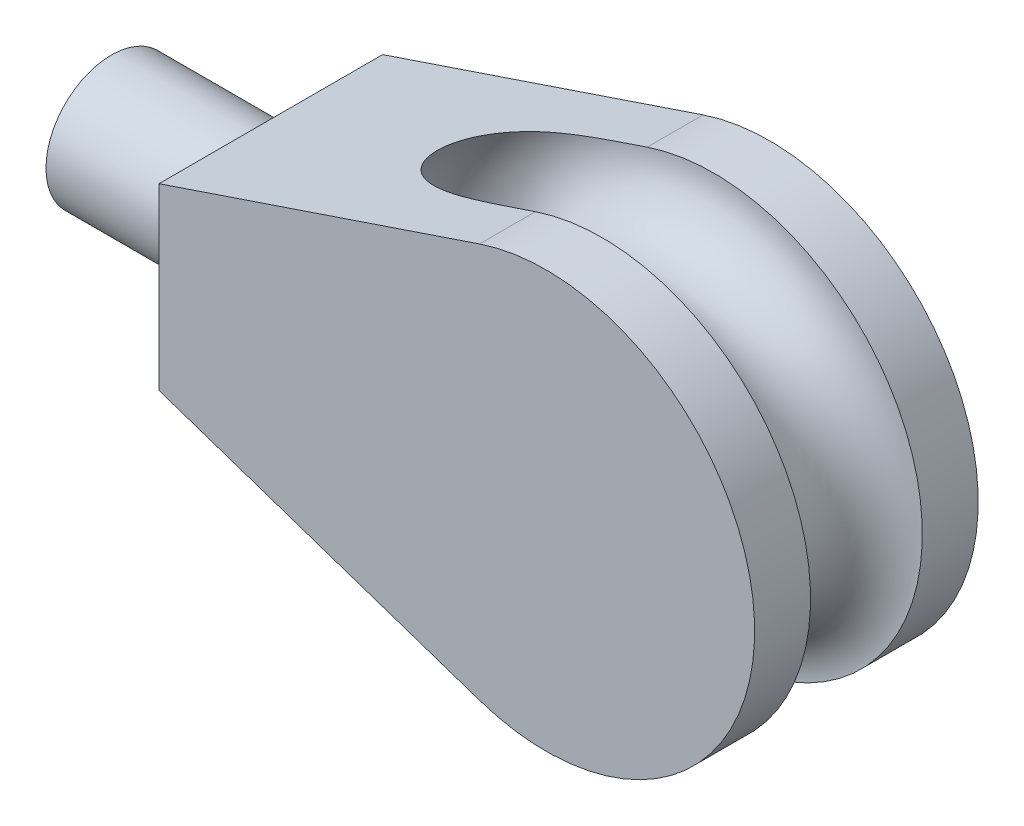
SolidWorks part; units mm, degrees
material "6061-T6 (SS)"
ref_plane "Front Plane" through (0, 0, 0) normal (0, 0, 1) x (1, 0, 0)
ref_plane "Top Plane" through (0, 0, 0) normal (0, 1, 0) x (1, 0, 0)
ref_plane "Right Plane" through (0, 0, 0) normal (1, 0, 0) x (0, 0, -1)
sketch "Sketch1" plane through (0, 0, 0) normal (0, 0, 1) x (1, 0, 0)
  line L0 (-27.4416, 6.35) -> (-27.4416, -6.35)
  line L1 (-27.4416, -6.35) -> (-4.722, -14.0084)
  line L2 (-27.4416, 6.35) -> (-4.722, 14.0084)
  arc A0 (-4.722, -14.0084) -> (-4.722, 14.0084) centre (0, 0) ccw
  point P5 (-27.4416, 0)
  dimension "D1" = 29.5656
  dimension "D2" = 12.7
  dimension "D3" = 108.628
extrude "Boss-Extrude1" add sketch "Sketch1" along normal mid plane 15.8496
sketch "Sketch2" plane through (-27.4416, 0, 0) normal (-1, 0, 0) x (0, 0, 1)
  circle A0 centre (0, 0) radius 4.6355
  dimension "D1" = 9.271
extrude "Boss-Extrude2" add sketch "Sketch2" along normal blind 11.303
sketch "Sketch6" plane through (0, 0, 0) normal (1, 0, 0) x (0, 0, -1)
  line L0 (7.9248, 14.7828) -> (-7.9248, 14.7828) construction
  line L1 (0, 0) -> (18.5567, 0) construction
  circle A0 centre (0, 14.7828) radius 3.9624
  dimension "D1" = 7.9248
revolve "Cut-Revolve1" cut sketch "Sketch6" angle 360 about L1
equation "\"Thick\"= \"in\""
